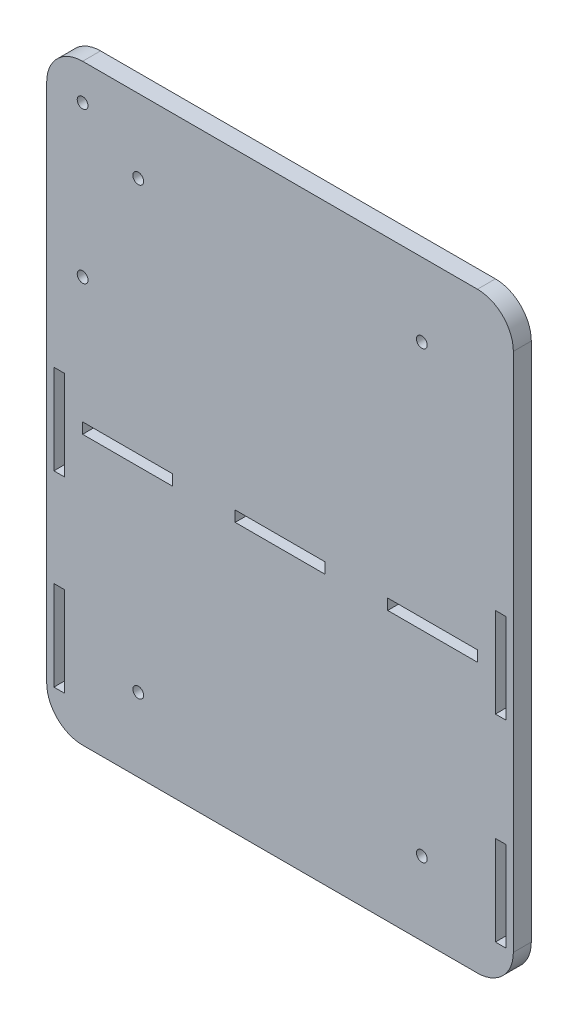
SolidWorks part; units mm, degrees
material "Acrílico (médio-alto impacto)"
ref_plane "Plano frontal" through (0, 0, 0) normal (0, 0, 1) x (1, 0, 0)
ref_plane "Plano superior" through (0, 0, 0) normal (0, 1, 0) x (1, 0, 0)
ref_plane "Plano direito" through (0, 0, 0) normal (1, 0, 0) x (0, 0, -1)
sketch "Esboço1" plane through (0, 0, 0) normal (0, 0, 1) x (1, 0, 0)
  line L1 (-49.2171, -36.3939) -> (60.7829, -36.3939)
  line L2 (-59.2171, -26.3939) -> (-59.2171, 118.6061)
  line L3 (-49.2171, 128.6061) -> (60.7829, 128.6061)
  line L4 (70.7829, -26.3939) -> (70.7829, 118.6061)
  arc A0 (-59.2171, 118.6061) -> (-49.2171, 128.6061) centre (-49.2171, 118.6061) cw
  arc A1 (60.7829, 128.6061) -> (70.7829, 118.6061) centre (60.7829, 118.6061) cw
  arc A2 (60.7829, -36.3939) -> (70.7829, -26.3939) centre (60.7829, -26.3939) ccw
  arc A3 (-49.2171, -36.3939) -> (-59.2171, -26.3939) centre (-49.2171, -26.3939) cw
  dimension "D1" = 10
extrude "Ressalto-extrusão1" add sketch "Esboço1" along normal blind 5
sketch "Esboço2" plane through (0, 0, 0) normal (0, 0, -1) x (-1, 0, 0)
  line L1 (-70.7829, -26.3939) -> (-70.7829, 118.6061) construction
  line L2 (59.2171, 118.6061) -> (59.2171, -26.3939) construction
  line L4 (-60.7829, 128.6061) -> (49.2171, 128.6061) construction
  circle A0 centre (33.7171, -15.8939) radius 1.5
  circle A1 centre (33.7171, 108.1061) radius 1.5
  circle A2 centre (-45.2829, -15.8939) radius 1.5
  circle A3 centre (-45.2829, 108.1061) radius 1.5
  dimension "D1" = 79
  dimension "D2" = 124
  dimension "D3" = 124
  dimension "D4" = 79
  dimension "D5" = 3
  dimension "D6" = 3
  dimension "D7" = 3
  dimension "D8" = 3
  dimension "D9" = 25.5
  dimension "D10" = 25.5
  dimension "D11" = 25.5
  dimension "D12" = 25.5
  dimension "D13" = 20.5
extrude "Corte-extrusão1" cut sketch "Esboço2" against normal blind 5
sketch "Esboço3" plane through (0, 0, 0) normal (0, 0, -1) x (-1, 0, 0)
  line L0 (-60.7829, 128.6061) -> (49.2171, 128.6061) construction
  line L1 (59.2171, 118.6061) -> (59.2171, -26.3939) construction
  circle A0 centre (49.2171, 118.6061) radius 1.5
  circle A1 centre (49.2171, 76.5561) radius 1.5
  dimension "D1" = 10
  dimension "D2" = 3
  dimension "D3" = 3
  dimension "D4" = 42.05
  dimension "D5" = 10
  dimension "D6" = 10
extrude "Corte-extrusão2" cut sketch "Esboço3" against normal through all
sketch "Esboço6" plane through (0, 0, 0) normal (0, 0, -1) x (-1, 0, 0)
  line L0 (49.2171, -36.3939) -> (-60.7829, -36.3939) construction
  line L1 (-68.7829, -26.3939) -> (-65.7829, -26.3939)
  line L2 (-68.7829, -26.3939) -> (-68.7829, -1.3939)
  line L3 (-68.7829, -1.3939) -> (-65.7829, -1.3939)
  line L4 (-65.7829, -26.3939) -> (-65.7829, -1.3939)
  line L5 (-68.7829, 28.6061) -> (-65.7829, 28.6061)
  line L6 (-68.7829, 28.6061) -> (-68.7829, 53.6061)
  line L7 (-68.7829, 53.6061) -> (-65.7829, 53.6061)
  line L8 (-65.7829, 28.6061) -> (-65.7829, 53.6061)
  line L9 (-60.7829, 38.6061) -> (-35.7829, 38.6061)
  line L10 (-60.7829, 38.6061) -> (-60.7829, 41.6061)
  line L11 (-60.7829, 41.6061) -> (-35.7829, 41.6061)
  line L12 (-35.7829, 38.6061) -> (-35.7829, 41.6061)
  line L13 (24.2171, 38.6061) -> (49.2171, 38.6061)
  line L14 (24.2171, 38.6061) -> (24.2171, 41.6061)
  line L15 (24.2171, 41.6061) -> (49.2171, 41.6061)
  line L16 (49.2171, 38.6061) -> (49.2171, 41.6061)
  line L17 (57.2171, 50.7869) -> (54.2171, 50.7869)
  line L18 (57.2171, 50.7869) -> (57.2171, 25.7869)
  line L19 (57.2171, 25.7869) -> (54.2171, 25.7869)
  line L20 (54.2171, 50.7869) -> (54.2171, 25.7869)
  line L21 (57.2171, -1.3939) -> (54.2171, -1.3939)
  line L22 (57.2171, -1.3939) -> (57.2171, -26.3939)
  line L23 (57.2171, -26.3939) -> (54.2171, -26.3939)
  line L24 (54.2171, -1.3939) -> (54.2171, -26.3939)
  line L25 (-70.7829, -26.3939) -> (-70.7829, 118.6061) construction
  line L26 (59.2171, 118.6061) -> (59.2171, -26.3939) construction
  line L28 (-18.2829, 38.6061) -> (6.7171, 38.6061)
  line L29 (-18.2829, 38.6061) -> (-18.2829, 41.6061)
  line L30 (-18.2829, 41.6061) -> (6.7171, 41.6061)
  line L31 (6.7171, 38.6061) -> (6.7171, 41.6061)
  point P26 (-70.7829, 46.1061)
  dimension "D1" = 10
  dimension "D2" = 30
  dimension "D3" = 25
  dimension "D4" = 25
  dimension "D5" = 2
  dimension "D6" = 3
  dimension "D7" = 3
  dimension "D8" = 2
  dimension "D9" = 10
  dimension "D10" = 25
  dimension "D11" = 3
  dimension "D12" = 10
  dimension "D13" = 3
  dimension "D14" = 25
  dimension "D15" = 25
  dimension "D16" = 3
  dimension "D17" = 17.5
  dimension "D18" = 10
  dimension "D19" = 25
  dimension "D20" = 3
  dimension "D21" = 3
  dimension "D22" = 25
  dimension "D23" = 2
  dimension "D24" = 2
  dimension "D25" = 75
  dimension "D26" = 75
  dimension "D27" = 75
extrude "Corte-extrusão4" cut sketch "Esboço6" against normal through all
